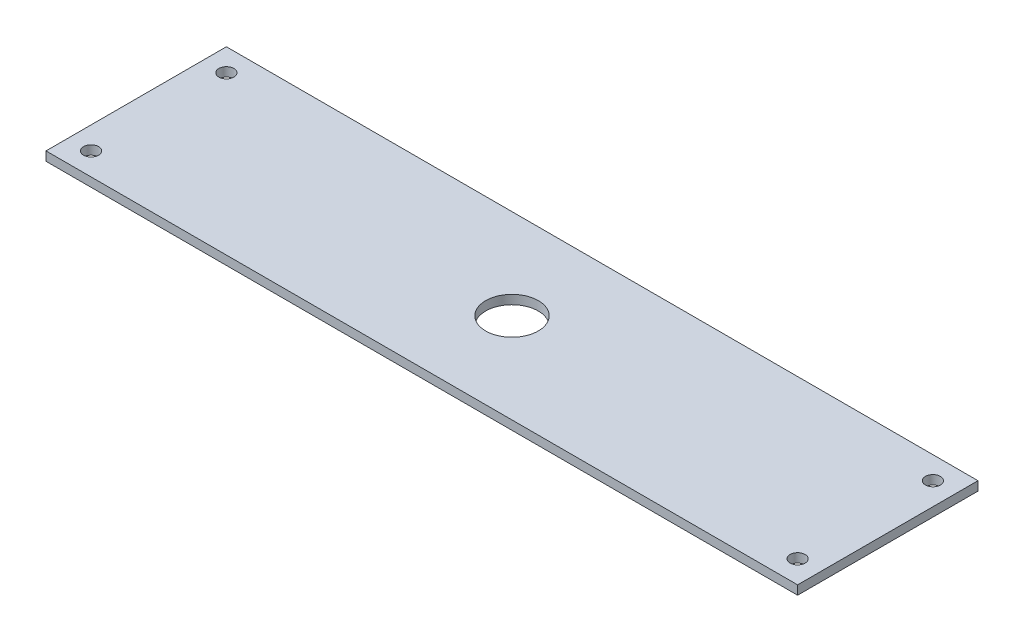
SolidWorks part; units mm, degrees
material "Plain Carbon Steel"
ref_plane "Front Plane" through (0, 0, 0) normal (0, 0, 1) x (1, 0, 0)
ref_plane "Top Plane" through (0, 0, 0) normal (0, 1, 0) x (1, 0, 0)
ref_plane "Right Plane" through (0, 0, 0) normal (1, 0, 0) x (0, 0, -1)
sketch "Sketch1" plane through (0, 0, 0) normal (0, 1, 0) x (1, 0, 0)
  line L0 (0, 0) -> (0, 155.1713) construction
  line L1 (-250, -60) -> (250, -60)
  line L2 (-250, -60) -> (-250, 60)
  line L3 (-250, 60) -> (250, 60)
  line L4 (250, -60) -> (250, 60)
  line L5 (-250, -60) -> (250, 60) construction
  line L6 (-250, 60) -> (250, -60) construction
  line L7 (0, 0) -> (-128.9943, 0) construction
  circle A0 centre (0, 0) radius 17.5
  circle A1 centre (-235, 45) radius 5
  circle A2 centre (-235, -45) radius 5
  circle A3 centre (235, 45) radius 5
  circle A4 centre (235, -45) radius 5
  point P0 (0, 0)
  dimension "D3" = 35
  dimension "D4" = 470
  dimension "D5" = 10
  dimension "D6" = 90
  dimension "D1" = 500
  dimension "D2" = 120
extrude "Boss-Extrude1" add sketch "Sketch1" along normal mid plane 6
